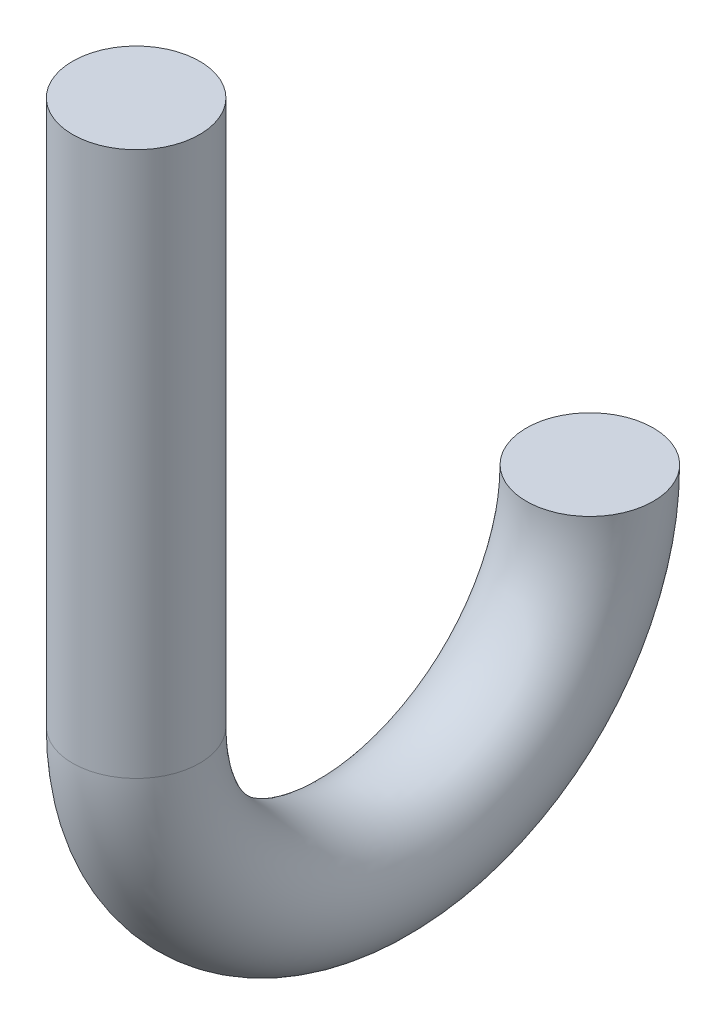
SolidWorks part; units mm, degrees
ref_plane "Front Plane" through (0, 0, 0) normal (0, 0, 1) x (1, 0, 0)
ref_plane "Top Plane" through (0, 0, 0) normal (0, 1, 0) x (1, 0, 0)
ref_plane "Right Plane" through (0, 0, 0) normal (1, 0, 0) x (0, 0, -1)
sketch "Sketch2" plane through (0, 0, 0) normal (1, 0, 0) x (0, 0, -1)
  line L0 (0, 30) -> (0, 0)
  arc A0 (0, 0) -> (25, 0) centre (12.5, 0) ccw
  point P4 (0, 0)
  point P5 (0, 0)
  dimension "D2" = 12.5
  dimension "D1" = 30
ref_plane "Plane1" through (0, 30, 0) normal (0, 1, 0) x (1, 0, 0)
sketch "Sketch3" plane through (0, 30, 0) normal (0, 1, 0) x (1, 0, 0)
  circle A0 centre (0, 0) radius 3.5
  dimension "D1" = 7
sweep "Sweep1" add profiles "Sketch3" path "Sketch2"
